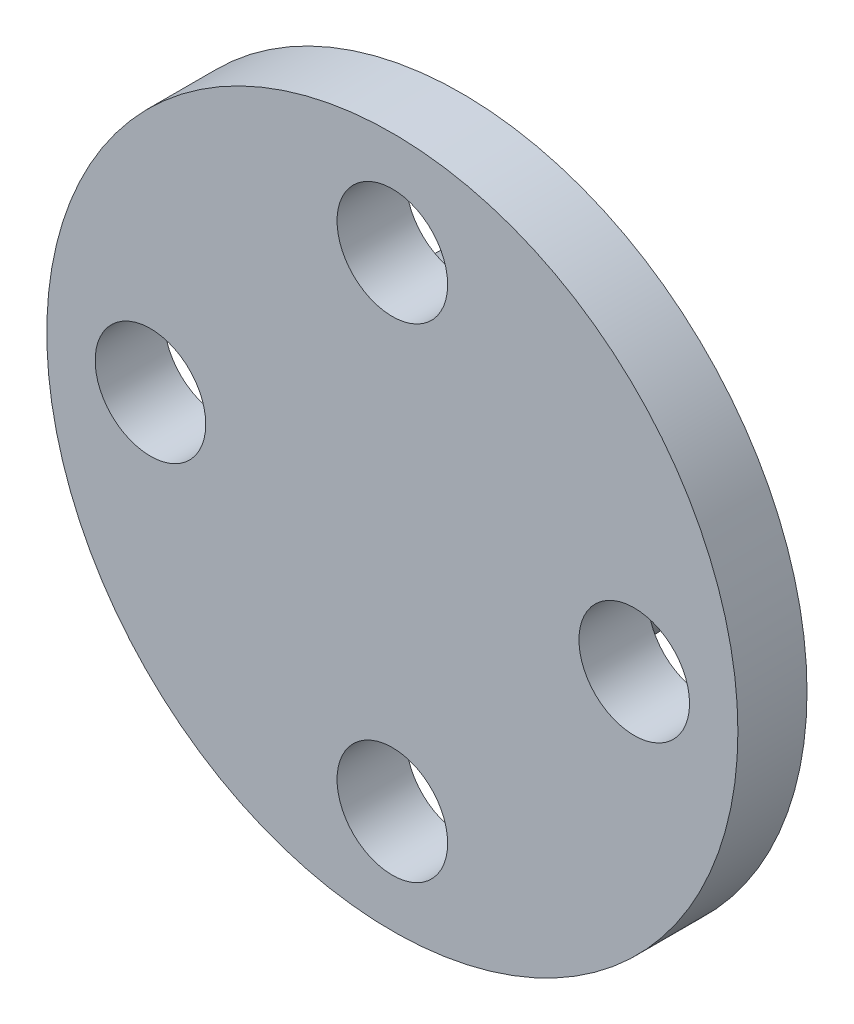
SolidWorks part; units mm, degrees
ref_plane "前视基准面" through (0, 0, 0) normal (0, 0, 1) x (1, 0, 0)
ref_plane "上视基准面" through (0, 0, 0) normal (0, 1, 0) x (1, 0, 0)
ref_plane "右视基准面" through (0, 0, 0) normal (1, 0, 0) x (0, 0, -1)
sketch "草图1" plane through (0, 0, 0) normal (0, 0, 1) x (1, 0, 0)
  circle A0 centre (0, 0) radius 10
  circle A2 centre (0, 7) radius 1.6
  circle A3 centre (7, 0) radius 1.6
  circle A4 centre (0, -7) radius 1.6
  circle A5 centre (-7, 0) radius 1.6
  point P15 (0, 0)
  dimension "D1" = 20
  dimension "D3" = 3.2
extrude "凸台-拉伸1" add sketch "草图1" along normal blind 2
sketch "草图2" plane through (0, 0, 0) normal (0, 0, -1) x (-1, 0, 0)
  circle A0 centre (0, 0) radius 4.5
  circle A1 centre (0, 0) radius 2.75
  dimension "D1" = 9
  dimension "D2" = 5.5
extrude "凸台-拉伸2" add sketch "草图2" along normal blind 2.5
